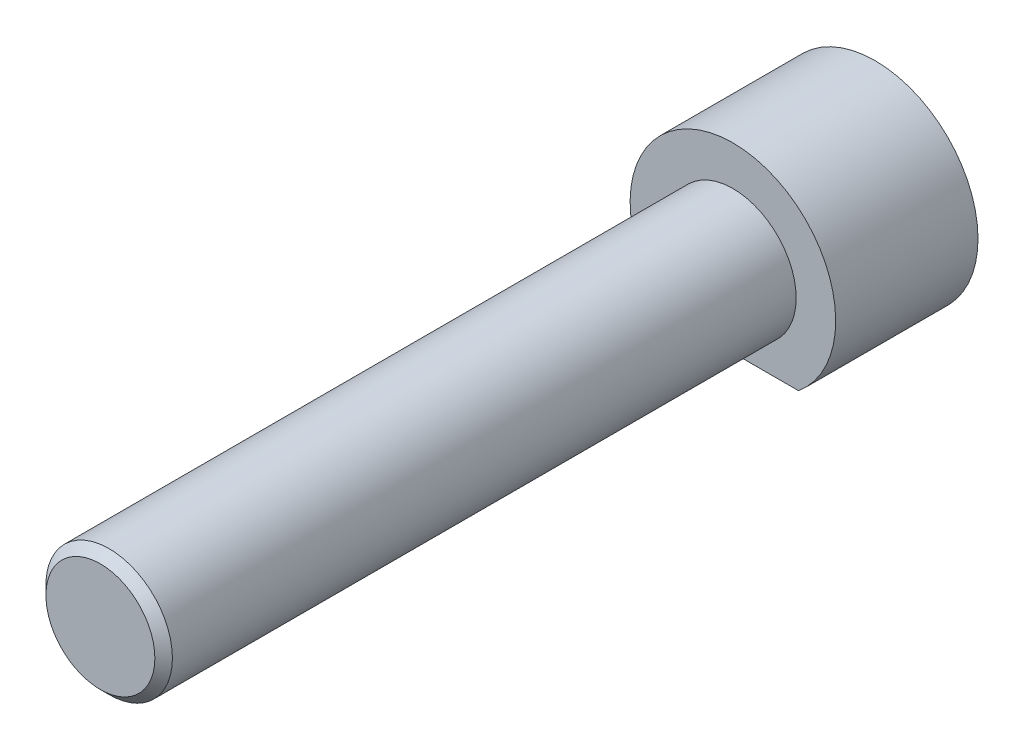
SolidWorks part; units mm, degrees
material "Сталь"
ref_plane "Спереди" through (0, 0, 0) normal (0, 0, 1) x (1, 0, 0)
ref_plane "Сверху" through (0, 0, 0) normal (0, 1, 0) x (1, 0, 0)
ref_plane "Справа" through (0, 0, 0) normal (1, 0, 0) x (0, 0, -1)
sketch "Эскиз1" plane through (0, 0, 0) normal (0, 0, 1) x (1, 0, 0)
  line L0 (-4.1533, -5) -> (4.1533, -5)
  circle A0 centre (0, 0) radius 6.5
  dimension "D1" = 13
  dimension "D2" = 5
extrude "Бобышка-Вытянуть1" add sketch "Эскиз1" along normal blind 9 contours L0 A0
sketch "Эскиз2" plane through (0, 0, 9) normal (0, 0, 1) x (1, 0, 0)
  circle A0 centre (0, 0) radius 4
  dimension "D1" = 8
extrude "Бобышка-Вытянуть2" add sketch "Эскиз2" along normal blind 40
cosmetic thread "Условное изображение резьбы1" parameters "D1"=8, "D2"=6.891
chamfer "Фаска1" distance 0.5545 angle 45 1 edges at (4, 0, 49)
